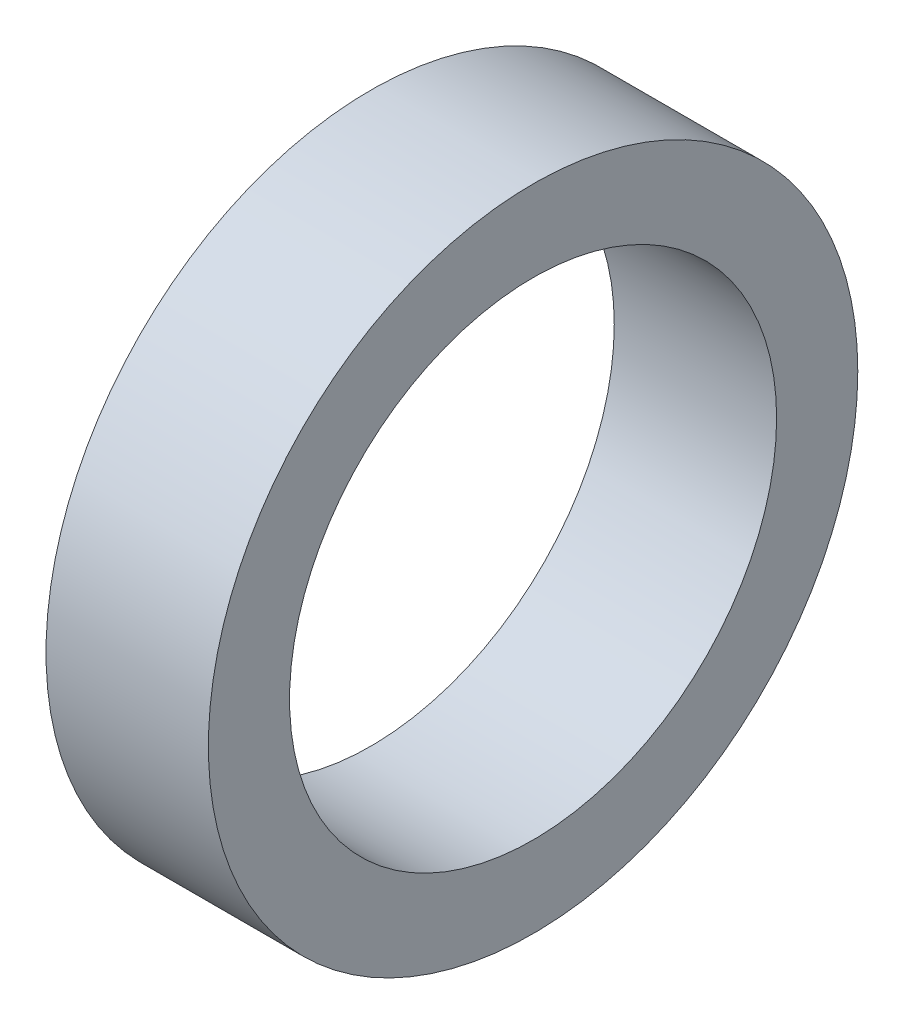
SolidWorks part; units mm, degrees
material "6061-T6 (SS)"
ref_plane "Front" through (0, 0, 0) normal (0, 0, 1) x (1, 0, 0)
ref_plane "Top" through (0, 0, 0) normal (0, 1, 0) x (1, 0, 0)
ref_plane "Right" through (0, 0, 0) normal (1, 0, 0) x (0, 0, -1)
sketch "Sketch1" plane through (0, 0, 0) normal (1, 0, 0) x (0, 0, -1)
  line L0 (9.525, 0) -> (12.7, 0) construction
  line L1 (9.525, 0) -> (12.7, 0) construction
  line L2 (11.1125, 0) -> (11.1125, 1.0672) construction
  circle A0 centre (0, 0) radius 12.7
  circle A1 centre (0, 0) radius 9.525
  point P4 (12.7, 0)
  point P5 (9.525, 0)
  dimension "OD" = 25.4
  dimension "ID" = 19.05
  dimension "Wall Thickness" = 3.175
sketch "Sketch2" plane through (0, 0, 0) normal (0, 0, 1) x (1, 0, 0)
  line L0 (-3.175, 0) -> (3.175, 0) construction
  point P2 (28.575, 0)
  point P3 (-28.575, 0)
  dimension "D1" = 31.75
  dimension "D2" = 31.75
sketch "Sketch3" plane through (0, 0, 0) normal (1, 0, 0) x (0, 0, -1)
  circle A0 centre (0, 0) radius 9.525 construction
  circle A1 centre (0, 0) radius 12.7 construction
  circle A2 centre (0, 0) radius 9.525
  circle A3 centre (0, 0) radius 12.7
extrude "Boss-Extrude1" add sketch "Sketch3" along normal mid plane 6.35
equation "\"D1@Boss-Extrude1\"=\"Length@Sketch2\""
equation "\"D1@Sketch2\"=\"OD@Sketch1\"*1.25"
equation "\"D2@Sketch2\"=\"D1@Sketch2\""
